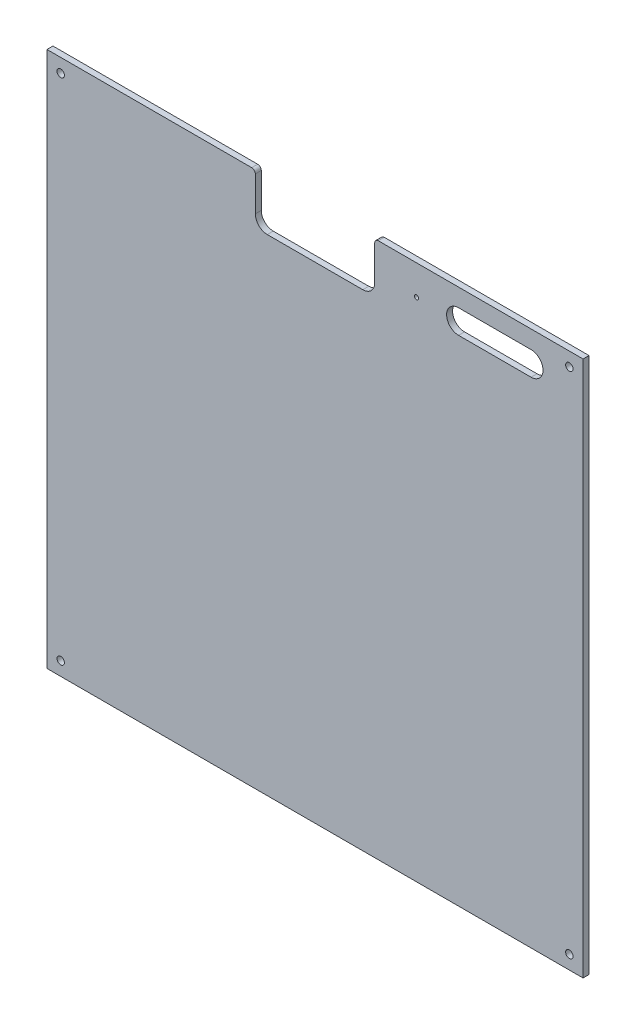
SolidWorks part; units mm, degrees
material "ABS PC"
ref_plane "Piano frontale" through (0, 0, 0) normal (0, 0, 1) x (1, 0, 0)
ref_plane "Piano superiore" through (0, 0, 0) normal (0, 1, 0) x (1, 0, 0)
ref_plane "Piano destro" through (0, 0, 0) normal (1, 0, 0) x (0, 0, -1)
sketch "Schizzo1" plane through (0, 0, 0) normal (0, 0, 1) x (1, 0, 0)
  line L0 (0, 0) -> (0, 449)
  line L1 (0, 449) -> (171.5, 449)
  line L2 (449, 449) -> (449, 0)
  line L3 (449, 0) -> (0, 0)
  line L4 (174.5, 446) -> (174.5, 417)
  line L5 (184.5, 407) -> (264.5, 407)
  line L6 (274.5, 417) -> (274.5, 446)
  line L7 (277.5, 449) -> (449, 449)
  line L8 (154.5, 424) -> (294.5, 424) construction
  line L9 (224.5, 379) -> (224.5, 419) construction
  line L10 (344.7159, 424) -> (405.4404, 424) construction
  line L11 (344.7159, 434) -> (405.4404, 434)
  line L12 (344.7159, 414) -> (405.4404, 414)
  line L13 (0, 224.5) -> (449, 224.5) construction
  line L23 (73.9219, 399) -> (73.9219, 449) construction
  line L24 (174.5, 431.5) -> (314.5, 431.5) construction
  arc A0 (174.5, 417) -> (184.5, 407) centre (184.5, 417) ccw
  arc A1 (274.5, 417) -> (264.5, 407) centre (264.5, 417) cw
  circle A2 centre (11.5, 11.5) radius 3.1
  circle A3 centre (437.5, 11.5) radius 3.1
  circle A4 centre (437.5, 437.5) radius 3.1
  circle A5 centre (11.5, 437.5) radius 3.1
  circle A6 centre (309.5, 424) radius 1.75
  arc A7 (277.5, 449) -> (274.5, 446) centre (277.5, 446) ccw
  arc A8 (344.7159, 434) -> (344.7159, 414) centre (344.7159, 424) ccw
  arc A9 (405.4404, 414) -> (405.4404, 434) centre (405.4404, 424) ccw
  arc A10 (174.5, 446) -> (171.5, 449) centre (171.5, 446) ccw
  point P11 (174.5, 407)
  point P14 (274.5, 407)
  point P33 (375.0781, 424)
  point P44 (174.5, 449)
  dimension "D5" = 10
  dimension "D6" = 11.5
  dimension "D7" = 11.5
  dimension "D8" = 6.2
  dimension "D9" = 3.5
  dimension "D10" = 35
  dimension "D12" = 3
  dimension "D1" = 449
  dimension "D2" = 449
  dimension "D3" = 100
  dimension "D4" = 42
  dimension "D11" = 20
  dimension "D21" = 25
extrude "Estrusione-Estrusione1" add sketch "Schizzo1" along normal blind 5
